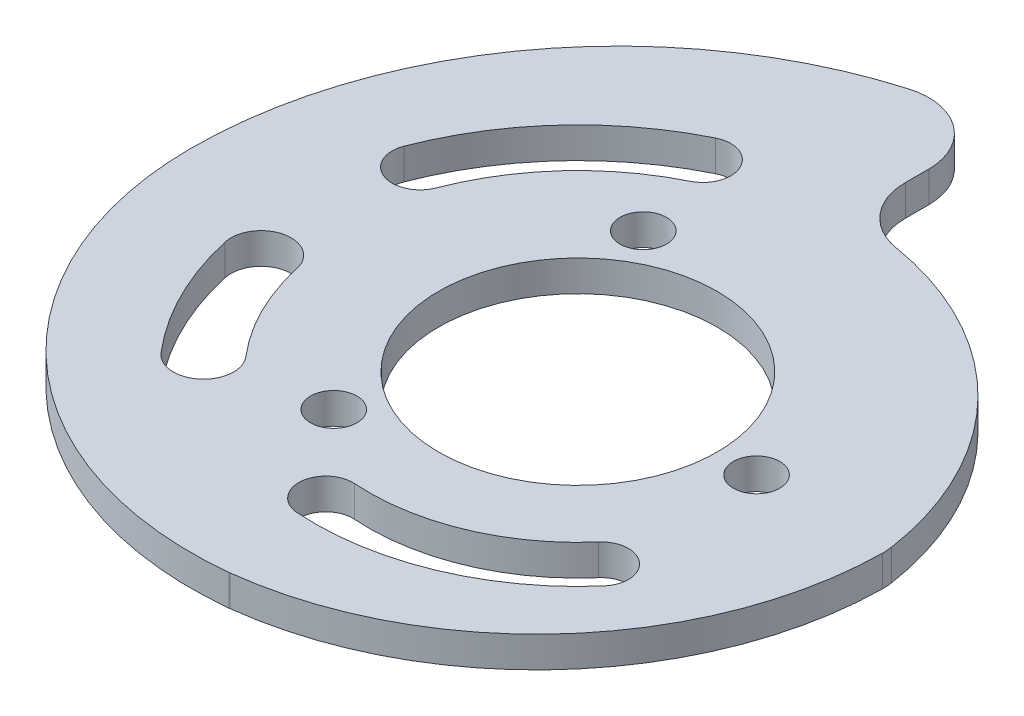
SolidWorks part; units mm, degrees
ref_plane "Front Plane" through (0, 0, 0) normal (0, 0, 1) x (1, 0, 0)
ref_plane "Top Plane" through (0, 0, 0) normal (0, 1, 0) x (1, 0, 0)
ref_plane "Right Plane" through (0, 0, 0) normal (1, 0, 0) x (0, 0, -1)
sketch "Sketch1" plane through (0, 0, 0) normal (0, 1, 0) x (1, 0, 0)
  line L0 (0, 0) -> (0, -27.5) construction
  line L1 (0, 0) -> (27.5, 0) construction
  line L2 (0, 0) -> (-27.5, 0) construction
  line L3 (0, 27.5) -> (0, 17.5)
  circle A0 centre (0, 0) radius 17.5 construction
  circle A1 centre (0, 0) radius 27.5 construction
  circle A2 centre (0, 0) radius 20 construction
  circle A3 centre (0, 0) radius 22.5 construction
  circle A4 centre (0, 0) radius 25 construction
  arc A5 (0, 27.5) -> (-25, 0) centre (2.625, 0) ccw
  arc A6 (-25, 0) -> (0, -22.5) centre (-2.375, 0) ccw
  arc A7 (0, -22.5) -> (20, 0) centre (-2.6563, 0) ccw
  arc A8 (20, 0) -> (0, 17.5) centre (0, -2.6786) ccw
  dimension "D1" = 10
  dimension "D5" = 55
  dimension "D2" = 2.5
  dimension "D3" = 2.5
  dimension "D4" = 2.5
extrude "Boss-Extrude1" add sketch "Sketch1" along normal blind 2
sketch "Sketch2" plane through (0, 2, 0) normal (0, 1, 0) x (1, 0, 0)
  circle A0 centre (0, 0) radius 9
  dimension "D1" = 18
extrude "Cut-Extrude1" cut sketch "Sketch2" against normal through all
fillet "Fillet1" radius 4 4 edges at (0, 1, 22.5) (20, 1, 0) (0, 1, -17.5) (0, 1, -27.5)
sketch "Sketch4" plane through (0, 2, 0) normal (0, 1, 0) x (1, 0, 0)
  line L1 (-5.7735, 10) -> (-5.7735, -10) construction
  line L2 (-5.7735, -10) -> (11.547, 0) construction
  line L3 (11.547, 0) -> (-5.7735, 10) construction
  circle A0 centre (0, 0) radius 5.7735 construction
  circle A1 centre (-5.7735, 10) radius 1.5
  circle A2 centre (11.547, 0) radius 1.5
  circle A3 centre (-5.7735, -10) radius 1.5
  dimension "D1" = 3
  dimension "D2" = 20
extrude "Cut-Extrude2" cut sketch "Sketch4" against normal through all
sketch "Sketch5" plane through (0, 2, 0) normal (0, 1, 0) x (1, 0, 0)
  arc A0 (-16.7538, -3.7122) -> (-13.05, -11.1431) centre (0, 0) ccw construction
  arc A1 (-18.6518, -4.1328) -> (-14.5284, -12.4054) centre (0, 0) ccw
  arc A2 (-14.8559, -3.2917) -> (-11.5716, -9.8807) centre (0, 0) ccw
  arc A3 (-14.8559, -3.2917) -> (-18.6518, -4.1328) centre (-16.7538, -3.7122) ccw
  arc A4 (-14.5284, -12.4054) -> (-11.5716, -9.8807) centre (-13.05, -11.1431) ccw
  arc A5 (-1.0688, -15.2177) -> (11.5207, -9.9997) centre (0, 0) ccw construction
  arc A6 (-1.191, -16.9577) -> (12.838, -11.1431) centre (0, 0) ccw
  arc A7 (-0.9466, -13.4777) -> (10.2034, -8.8563) centre (0, 0) ccw
  arc A8 (-0.9466, -13.4777) -> (-1.191, -16.9577) centre (-1.0688, -15.2177) ccw
  arc A9 (12.838, -11.1431) -> (10.2034, -8.8563) centre (11.5207, -9.9997) ccw
  arc A10 (-7.8287, 15.9037) -> (-16.5478, 6.3551) centre (0, 0) ccw construction
  arc A11 (-8.6273, 17.5259) -> (-18.2357, 7.0033) centre (0, 0) ccw
  arc A12 (-7.0302, 14.2815) -> (-14.8599, 5.7069) centre (0, 0) ccw
  arc A13 (-7.0302, 14.2815) -> (-8.6273, 17.5259) centre (-7.8287, 15.9037) ccw
  arc A14 (-18.2357, 7.0033) -> (-14.8599, 5.7069) centre (-16.5478, 6.3551) ccw
  point P4 (-15.3581, -7.655)
  point P9 (5.841, -14.0927)
  point P14 (-13.09, 11.9528)
  point P25 (-13.2636, 13.0218)
  point P26 (-13.2636, 5.0938)
  point P27 (-15.3581, -7.655)
  point P28 (12.838, -11.1431)
extrude "Cut-Extrude3" cut sketch "Sketch5" against normal through all
